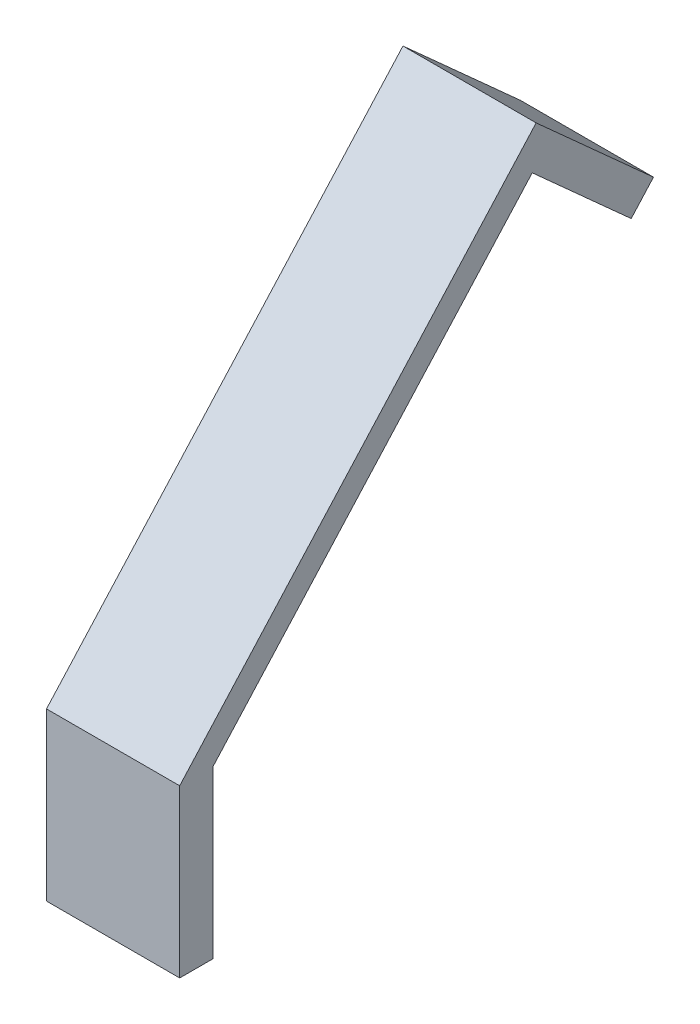
SolidWorks part; units mm, degrees
ref_plane "Front Plane" through (0, 0, 0) normal (0, 0, 1) x (1, 0, 0)
ref_plane "Top Plane" through (0, 0, 0) normal (0, 1, 0) x (1, 0, 0)
ref_plane "Right Plane" through (0, 0, 0) normal (1, 0, 0) x (0, 0, -1)
sketch "Sketch1" plane through (0, 0, 0) normal (1, 0, 0) x (0, 0, -1)
  line L0 (0, 0) -> (12.7, 0)
  line L1 (0, 0) -> (0, 63.5)
  line L2 (0, 63.5) -> (12.7, 63.5)
  line L3 (12.7, 0) -> (12.7, 63.5)
  line L4 (0, 63.5) -> (135.9673, 214.507)
  line L5 (135.9673, 214.507) -> (180.7329, 174.2)
  line L6 (180.7329, 174.2) -> (172.2349, 164.762)
  line L7 (172.2349, 164.762) -> (134.4831, 198.7539)
  line L8 (134.4831, 198.7539) -> (12.7, 63.5)
  point P8 (0, 0)
  point P9 (-90.8326, -97.3344)
  point P10 (0, 0)
  point P12 (148.3886, 148.1701)
  point P13 (0, 0)
  point P14 (12.7, 69.0825)
  point P15 (0, 0)
  point P16 (0, 0)
  point P17 (0, 0)
  point P18 (0, 0)
  point P19 (0, 0)
  point P20 (112.831, 200.4454)
  point P21 (0, 0)
  dimension "D1" = 12.7
  dimension "D2" = 63.5
  dimension "D3" = 203.2
  dimension "D4" = 50.8
  dimension "D5" = 90
  dimension "D6" = 138
extrude "Boss-Extrude1" add sketch "Sketch1" along normal blind 50.8 contours L8 L7 L6 L5 L4 L2 | L0 L3 L2 L1
